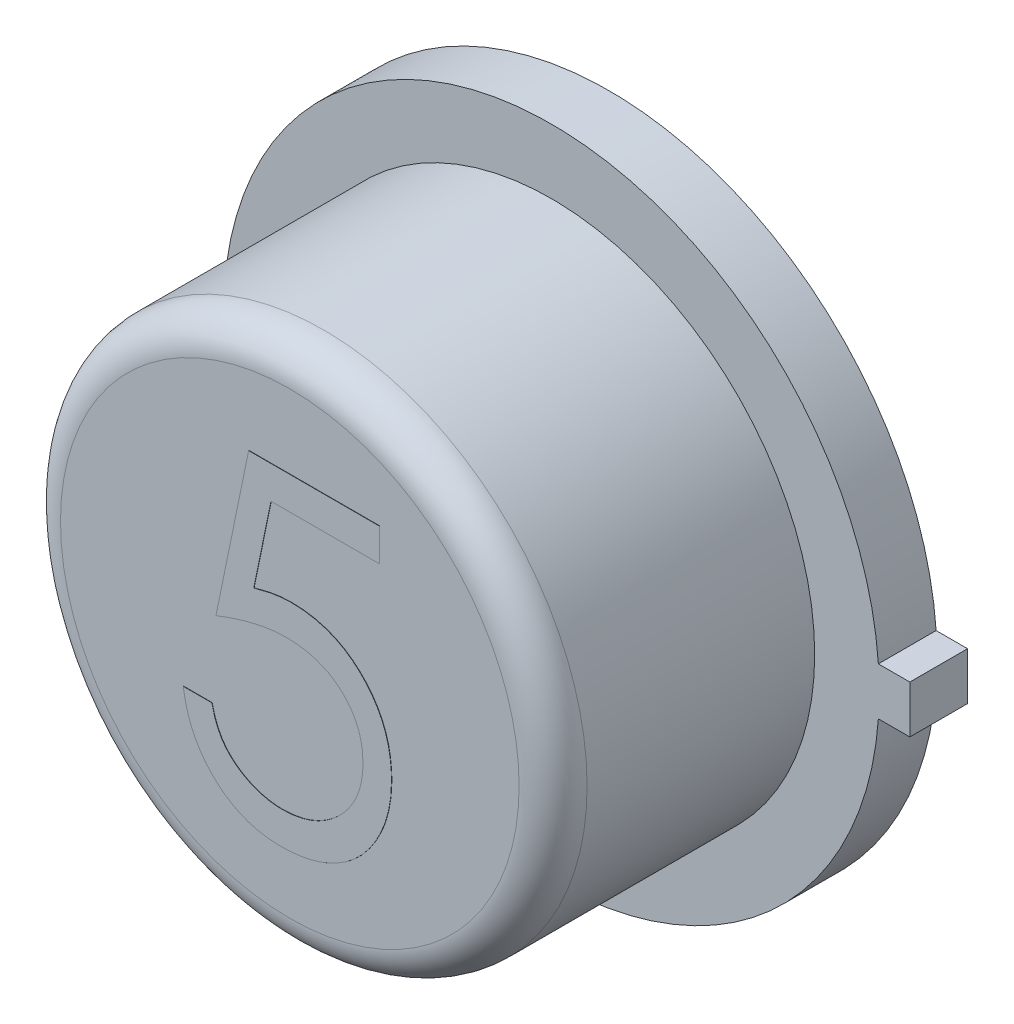
SolidWorks part; units mm, degrees
ref_plane "Front Plane" through (0, 0, 0) normal (0, 0, 1) x (1, 0, 0)
ref_plane "Top Plane" through (0, 0, 0) normal (0, 1, 0) x (1, 0, 0)
ref_plane "Right Plane" through (0, 0, 0) normal (1, 0, 0) x (0, 0, -1)
sketch "Sketch1" plane through (0, 0, 0) normal (0, 0, 1) x (1, 0, 0)
  line L1 (2.4511, 0.1778) -> (2.6797, 0.1778)
  line L3 (2.4511, -0.1778) -> (2.6797, -0.1778)
  line L4 (2.6797, 0.1778) -> (2.6797, -0.1778)
  line L5 (2.4511, 0.1778) -> (2.4444, 0.1778)
  line L6 (2.4511, -0.1778) -> (2.4446, -0.1778)
  arc A0 (2.4446, 0.1778) -> (2.4446, -0.1778) centre (0, 0) ccw
  dimension "D1" = 4.9022
  dimension "D2" = 0.3556
  dimension "D3" = 0.2286
extrude "Boss-Extrude1" add sketch "Sketch1" along normal blind 0.4318
sketch "Sketch2" plane through (0, 0, 0.4318) normal (0, 0, 1) x (1, 0, 0)
  circle A0 centre (0, 0) radius 1.9685
  dimension "D1" = 3.937
extrude "Boss-Extrude2" add sketch "Sketch2" along normal blind 1.9558
sketch "Sketch3" plane through (0, 0, 0) normal (0, 0, -1) x (-1, 0, 0)
  circle A0 centre (0, 0) radius 1.7576
extrude "Boss-Extrude3" add sketch "Sketch3" along normal blind 0.0025
fillet "Fillet1" radius 0.254 1 edges at (1.9685, 0, 2.3876)
sketch "Sketch4" plane through (0, 0, 2.3876) normal (0, 0, 1) x (1, 0, 0)
  line L0 (-1.2065, -1.2181) -> (1.2065, -1.2181) construction
  circle A0 centre (0, 0) radius 1.7145 construction
  text T0 "5" font "Century Gothic" height in points 9
  dimension "D1" = 2.413
extrude "Boss-Extrude6" add sketch "Sketch4" along normal blind 0.0025
